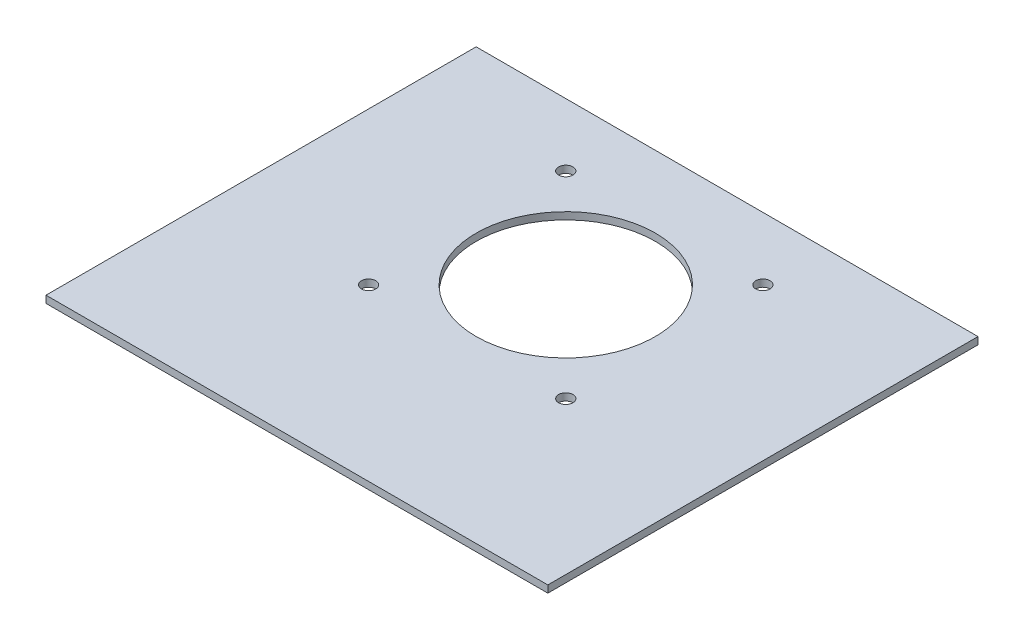
SolidWorks part; units mm, degrees
ref_plane "Спереди" through (0, 0, 0) normal (0, 0, 1) x (1, 0, 0)
ref_plane "Сверху" through (0, 0, 0) normal (0, 1, 0) x (1, 0, 0)
ref_plane "Справа" through (0, 0, 0) normal (1, 0, 0) x (0, 0, -1)
sketch "Эскиз1" plane through (0, 0, 0) normal (0, 1, 0) x (1, 0, 0)
  line L1 (-70, 45) -> (70, 45)
  line L2 (-70, 45) -> (-70, -75)
  line L3 (-70, -75) -> (70, -75)
  line L4 (70, 45) -> (70, -75)
  circle A0 centre (27.5, 27.5) radius 2
  circle A1 centre (-27.5, 27.5) radius 2
  circle A2 centre (-27.5, -27.5) radius 2
  circle A3 centre (27.5, -27.5) radius 2
  circle A4 centre (0, 0) radius 25
  dimension "D1" = 2
  dimension "D2" = 2
extrude "Бобышка-Вытянуть1" add sketch "Эскиз1" along normal blind 2
